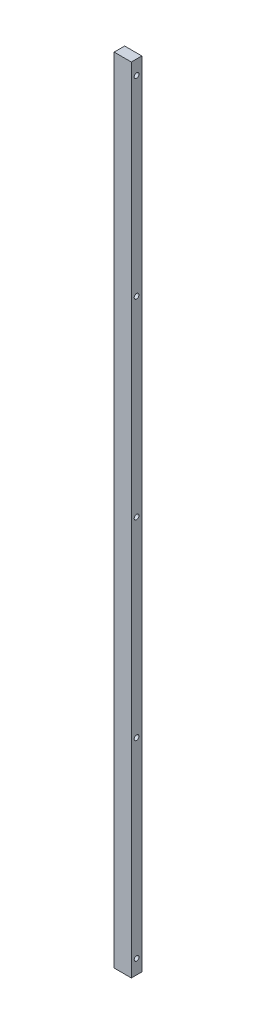
SolidWorks part; units mm, degrees
material "A3钢"
ref_plane "前视基准面" through (0, 0, 0) normal (0, 0, 1) x (1, 0, 0)
ref_plane "上视基准面" through (0, 0, 0) normal (0, 1, 0) x (1, 0, 0)
ref_plane "右视基准面" through (0, 0, 0) normal (1, 0, 0) x (0, 0, -1)
sketch "草图1" plane through (0, 0, 0) normal (0, 0, 1) x (1, 0, 0)
  line L1 (-9, -415) -> (9, -415)
  line L2 (-9, -415) -> (-9, 415)
  line L3 (-9, 415) -> (9, 415)
  line L4 (9, -415) -> (9, 415)
  line L5 (-9, -415) -> (9, 415) construction
  line L6 (-9, 415) -> (9, -415) construction
  point P0 (0, 0)
  dimension "D1" = 18
  dimension "D2" = 830
extrude "凸台-拉伸1" add sketch "草图1" along normal mid plane 11
sketch "草图9" plane through (9, 0, 0) normal (1, 0, 0) x (0, 0, -1)
  line L0 (-219.6012, 0) -> (285.8959, 0) construction
  line L1 (0, 400) -> (0, 200) construction
  line L2 (0, 200) -> (0, -200) construction
  line L3 (0, -400) -> (0, -200) construction
  point P7 (0, 0)
  dimension "D1" = 200
  dimension "D2" = 200
hole_wizard "M6 螺纹孔1" positions "3D草图1" profile "草图11" tap size "M6" standard "GB"
sketch3d "3D草图1"
  point P0 (9, -400, 0)
  point P3 (9, -200, 0)
  point P6 (9, 0, 0)
  point P9 (9, 200, 0)
  point P12 (9, 400, 0)
sketch "草图11" plane through (9, -400, 0) normal (0, 1, 0) x (0, 0, -1)
  line L0 (0, 0) -> (0, 16.5022)
  line L1 (0, 16.5022) -> (2.5, 15)
  line L2 (2.5, 15) -> (2.5, 0)
  line L5 (2.5, 0) -> (0, 0)
  line L10 (0, 16.5022) -> (-2.5, 15) construction
  line L11 (0, -6.35) -> (0, 107.95) construction
  dimension "螺纹孔钻头直径" = 5
  dimension "螺纹孔钻头深度" = 15
  dimension "导头角度" = 118
cosmetic thread "孔螺蚊线1"
cosmetic thread "孔螺蚊线2"
cosmetic thread "孔螺蚊线3"
cosmetic thread "孔螺蚊线4"
cosmetic thread "孔螺蚊线5"
